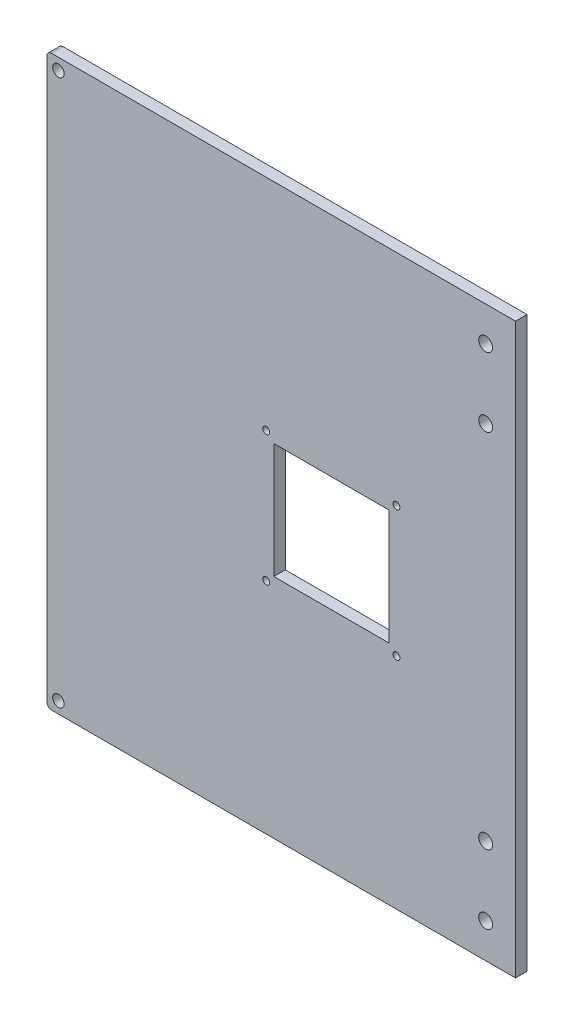
SolidWorks part; units mm, degrees
material "Glass"
ref_plane "Front Plane" through (0, 0, 0) normal (0, 0, 1) x (1, 0, 0)
ref_plane "Top Plane" through (0, 0, 0) normal (0, 1, 0) x (1, 0, 0)
ref_plane "Right Plane" through (0, 0, 0) normal (1, 0, 0) x (0, 0, -1)
sketch "Sketch1" plane through (0, 0, 0) normal (0, 0, 1) x (1, 0, 0)
  line L0 (-123.5, 121.5) -> (-123.5, -121.5)
  line L1 (-121.5, -123.5) -> (121.5, -123.5)
  line L2 (123.5, -121.5) -> (123.5, 121.5)
  line L3 (121.5, 123.5) -> (-121.5, 123.5)
  line L4 (0, 0) -> (0, 144.9076) construction
  line L5 (0, 0) -> (173.8049, 0) construction
  arc A0 (-123.5, -121.5) -> (-121.5, -123.5) centre (-121.5, -121.5) ccw
  arc A1 (121.5, -123.5) -> (123.5, -121.5) centre (121.5, -121.5) ccw
  arc A2 (123.5, 121.5) -> (121.5, 123.5) centre (121.5, 121.5) ccw
  arc A3 (-123.5, 121.5) -> (-121.5, 123.5) centre (-121.5, 121.5) cw
  circle A4 centre (-118.5, 118.5) radius 2.5
  circle A8 centre (118.5, 118.5) radius 2.5
  circle A9 centre (118.5, -118.5) radius 2.5
  circle A10 centre (-118.5, -118.5) radius 2.5
  dimension "D5" = 2
  dimension "D6" = 5
  dimension "D1" = 247
  dimension "D2" = 123.5
  dimension "D3" = 123.5
  dimension "D4" = 247
  dimension "D10" = 5
  dimension "D11" = 5
extrude "Boss-Extrude1" add sketch "Sketch1" along normal blind 5
sketch "Sketch2" plane through (0, 0, 0) normal (0, 0, -1) x (-1, 0, 0)
  line L0 (-25, 25) -> (-25, -25)
  line L1 (-25, -25) -> (25, -25)
  line L2 (25, -25) -> (25, 25)
  line L3 (25, 25) -> (-25, 25)
  line L4 (0, 0) -> (74.833, 0) construction
  line L5 (0, 0) -> (55.9239, 55.9239) construction
  line L6 (0, 0) -> (0, 65.9297) construction
  circle A0 centre (28.2843, 28.2843) radius 1.5
  circle A1 centre (28.2843, -28.2843) radius 1.5
  circle A2 centre (-28.2843, -28.2843) radius 1.5
  circle A3 centre (-28.2843, 28.2843) radius 1.5
  dimension "D7" = 3
  dimension "D1" = 25
  dimension "D2" = 25
  dimension "D3" = 25
  dimension "D4" = 25
  dimension "D5" = 45
  dimension "D6" = 40
extrude "Cut-Extrude1" cut sketch "Sketch2" against normal blind 5
sketch "Sketch3" plane through (0, 0, 0) normal (0, 0, -1) x (-1, 0, 0)
  line L4 (-160, 150) -> (-160, -150)
  line L5 (-160, -150) -> (-80, -150)
  line L6 (-80, -150) -> (-80, 150)
  line L7 (-80, 150) -> (-160, 150)
  dimension "D1" = 80
  dimension "D2" = 80
  dimension "D3" = 150
  dimension "D4" = 300
extrude "Cut-Extrude2" cut sketch "Sketch3" against normal blind 10
sketch "Sketch5" plane through (0, 0, 0) normal (0, 0, -1) x (-1, 0, 0)
  line L0 (-80, 123.5) -> (121.5, 123.5) construction
  line L1 (-80, -123.5) -> (-80, 123.5) construction
  line L2 (0, 0) -> (-140.6023, 0) construction
  circle A0 centre (-67, 108.5) radius 3
  circle A1 centre (-67, 78.5) radius 3
  circle A4 centre (-67, -108.5) radius 3
  circle A5 centre (-67, -78.5) radius 3
  dimension "D3" = 6
  dimension "D4" = 6
  dimension "D1" = 45
  dimension "D2" = 30
  dimension "D5" = 13
  dimension "D6" = 13
extrude "Cut-Extrude4" cut sketch "Sketch5" against normal blind 10
sketch "Sketch4" plane through (0, 0, 0) normal (0, 0, -1) x (-1, 0, 0)
  line L0 (-80, 123.5) -> (-80, -123.5) construction
  line L1 (-121.5, 123.5) -> (-80, 123.5) construction
  line L2 (0, 0) -> (53.143, 0) construction
  circle A0 centre (-93, 78.5) radius 3
  circle A1 centre (-93, 108.5) radius 3
  circle A2 centre (-93, -78.5) radius 3
  circle A3 centre (-93, -108.5) radius 3
  dimension "D3" = 6
  dimension "D4" = 6
  dimension "D1" = 13
  dimension "D2" = 45
  dimension "D5" = 30
  dimension "D6" = 13
extrude "Cut-Extrude3" cut sketch "Sketch4" against normal blind 10
